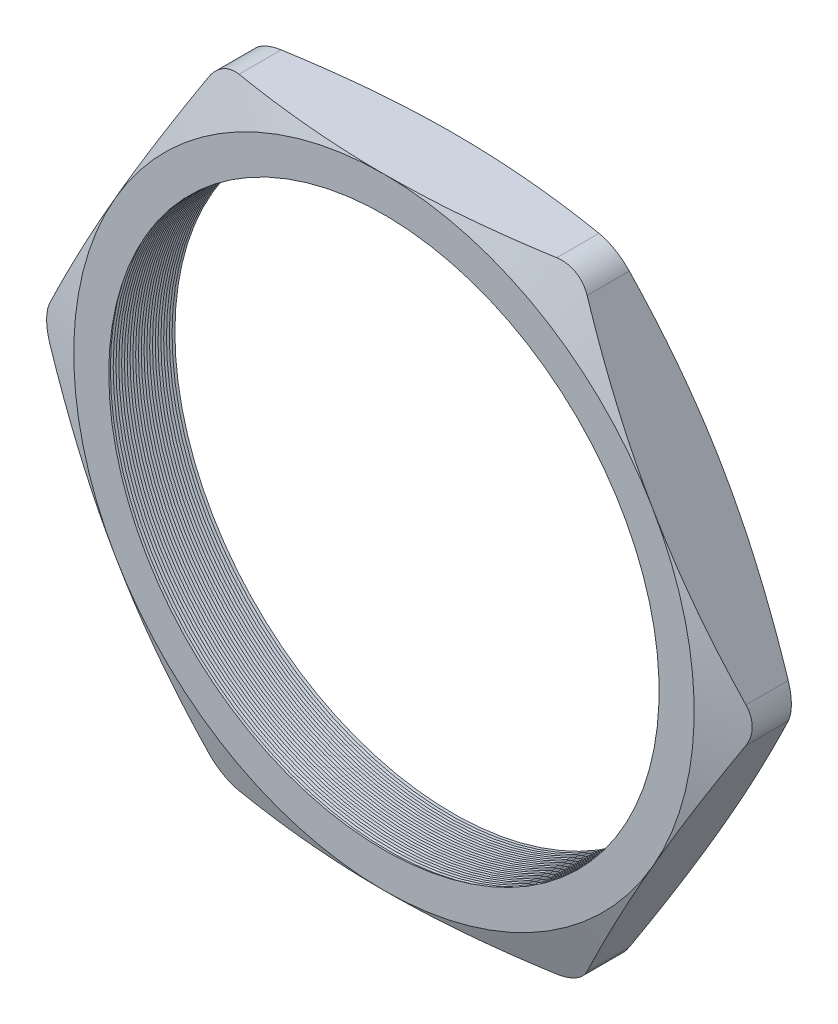
SolidWorks part; units mm, degrees
ref_plane "Front Plane" through (0, 0, 0) normal (0, 0, 1) x (1, 0, 0)
ref_plane "Top Plane" through (0, 0, 0) normal (0, 1, 0) x (1, 0, 0)
ref_plane "Right Plane" through (0, 0, 0) normal (1, 0, 0) x (0, 0, -1)
sketch "Sketch1" plane through (0, 0, 0) normal (0, 0, 1) x (1, 0, 0)
  line L1 (-25.9565, 0) -> (-12.9783, -22.479)
  line L2 (-12.9783, -22.479) -> (12.9783, -22.479)
  line L3 (12.9783, -22.479) -> (25.9565, 0)
  line L4 (25.9565, 0) -> (12.9783, 22.479)
  line L5 (12.9783, 22.479) -> (-12.9783, 22.479)
  line L6 (-12.9783, 22.479) -> (-25.9565, 0)
  circle A0 centre (0, 0) radius 22.479 construction
  circle A1 centre (0, 0) radius 19.939
  dimension "TS" = 39.878
  dimension "H" = 44.958
extrude "Extrude1" add sketch "Sketch1" along normal blind 5.08
fillet "Fillet1" radius 2.54 6 edges at (-12.9783, 22.479, 2.54) (-25.9565, 0, 2.54) (-12.9783, -22.479, 2.54) (12.9783, -22.479, 2.54) (25.9565, 0, 2.54) (12.9783, 22.479, 2.54)
sketch "Sketch2" plane through (0, 0, 5.08) normal (0, 0, 1) x (1, 0, 0)
  line L0 (11.5118, 22.479) -> (-11.5118, 22.479) construction
  circle A0 centre (0, 0) radius 22.479
extrude "Cut-Extrude1" cut sketch "Sketch2" against normal through all draft 70 flip side to cut
sketch "Sketch3" plane through (0, 0, 0) normal (0, 0, -1) x (-1, 0, 0)
  circle A0 centre (0, 0) radius 22.479
extrude "Cut-Extrude2" cut sketch "Sketch3" against normal through all draft 70 flip side to cut
sketch "Sketch4" plane through (0, 0, 0) normal (0, 1, 0) x (1, 0, 0)
  line L0 (-19.939, -5.08) -> (-19.939, -4.6401)
  line L2 (-19.939, -4.6401) -> (-20.32, -4.86)
  line L3 (-20.32, -4.86) -> (-19.939, -5.08)
  line L5 (-19.939, 0) -> (-19.939, -5.08) construction
  line L6 (-19.939, -5.08) -> (19.939, -5.08) construction
  dimension "D1" = 60
  dimension "D2" = 60
  dimension "D3" = 0.381
revolve "Cut-Revolve1" cut sketch "Sketch4" angle 360 about axis through (0, 0, 5.08) along (0, 0, -1)
pattern_linear "LPattern1" count 25 spacing 0.2032 along (0, 0, -1) of "Cut-Revolve1"
